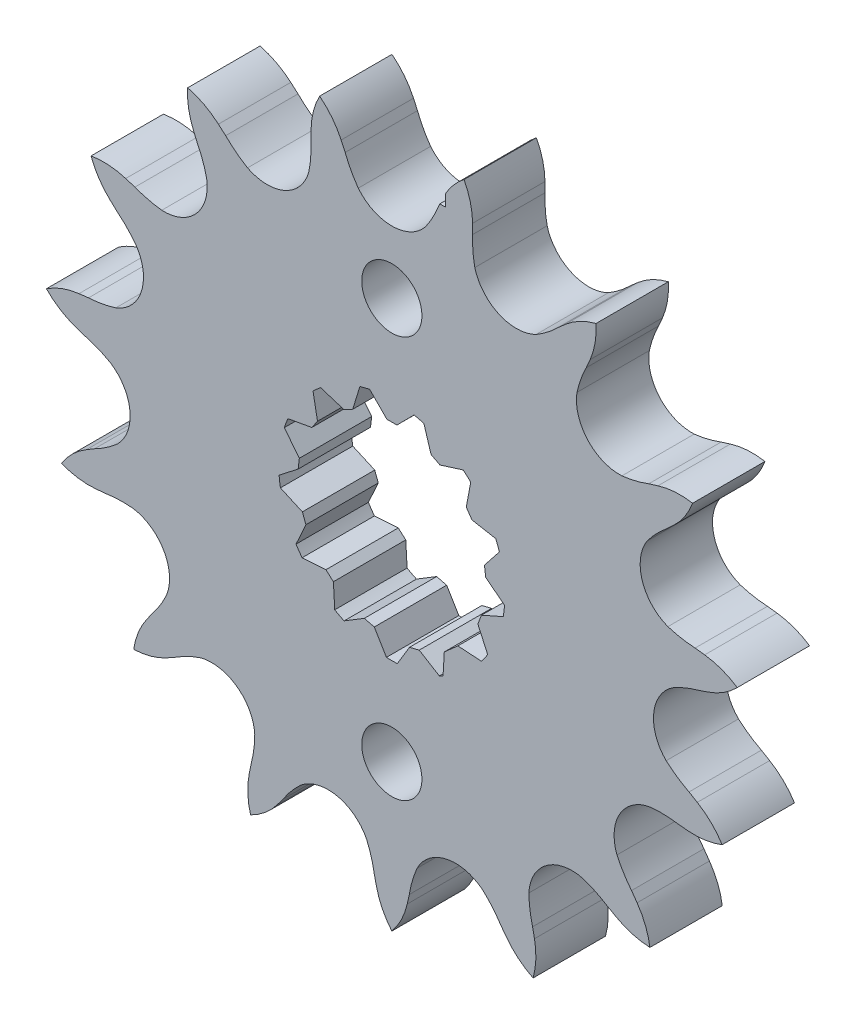
SolidWorks part; units mm, degrees
ref_plane "Front Plane" through (0, 0, 0) normal (0, 0, 1) x (1, 0, 0)
ref_plane "Top Plane" through (0, 0, 0) normal (0, 1, 0) x (1, 0, 0)
ref_plane "Right Plane" through (0, 0, 0) normal (1, 0, 0) x (0, 0, -1)
sketch "Sketch1" plane through (0, 0, 0) normal (0, 0, 1) x (1, 0, 0)
  line L0 (0, 0) -> (0, 90.9513)
  line L1 (27.8443, 30.54) -> (-27.8443, 30.54)
  line L2 (5.34, 0) -> (5.34, 90.9513)
  line L3 (27.8443, 34.869) -> (-27.8443, 34.869)
  line L4 (5.34, 34.869) -> (-3.3441, 27.8368)
  line L5 (5.34, 34.869) -> (-4.6509, 30.2665)
  line L6 (-4.6509, 30.2665) -> (-5.0517, 31.1366)
  line L7 (-11.77, 0) -> (-11.77, 90.9513)
  line L8 (27.8443, 28.037) -> (-27.8443, 28.037)
  line L9 (0, 0) -> (-8.8556, 41.6622)
  line L10 (4.6509, 30.2665) -> (5.0517, 31.1366)
  line L11 (16.5593, 25.7582) -> (17.2794, 26.39)
  line L12 (8.0617, 29.5415) -> (8.0495, 30.4995)
  line L13 (25.6045, 16.796) -> (26.5193, 17.0803)
  line L14 (19.3804, 23.7085) -> (19.7588, 24.5886)
  line L15 (30.2224, 4.9296) -> (31.1738, 4.8173)
  line L16 (27.348, 13.7761) -> (28.0517, 14.4262)
  line L17 (29.6146, -7.7891) -> (30.438, -8.2787)
  line L18 (30.5869, 1.4617) -> (31.4941, 1.7694)
  line L19 (23.8862, -19.161) -> (24.4393, -19.9432)
  line L20 (28.537, -11.1055) -> (29.491, -11.1934)
  line L21 (14.0276, -27.2198) -> (14.2148, -28.1594)
  line L22 (21.5528, -21.7524) -> (22.3886, -22.2208)
  line L23 (1.7435, -30.5721) -> (1.5324, -31.5065)
  line L24 (10.842, -28.6382) -> (11.415, -29.4059)
  line L25 (-10.842, -28.6382) -> (-11.415, -29.4059)
  line L26 (-1.7435, -30.5721) -> (-1.5324, -31.5065)
  line L27 (-21.5528, -21.7524) -> (-22.3886, -22.2208)
  line L28 (-14.0276, -27.2198) -> (-14.2148, -28.1594)
  line L29 (-28.537, -11.1055) -> (-29.491, -11.1934)
  line L30 (-23.8862, -19.161) -> (-24.4393, -19.9432)
  line L31 (-30.5869, 1.4617) -> (-31.4941, 1.7694)
  line L32 (-29.6146, -7.7891) -> (-30.438, -8.2787)
  line L33 (-27.348, 13.7761) -> (-28.0517, 14.4262)
  line L34 (-30.2224, 4.9296) -> (-31.1738, 4.8173)
  line L35 (-19.3804, 23.7085) -> (-19.7588, 24.5886)
  line L36 (-25.6045, 16.796) -> (-26.5193, 17.0803)
  line L37 (-8.0617, 29.5415) -> (-8.0495, 30.4995)
  line L38 (-16.5593, 25.7582) -> (-17.2794, 26.39)
  arc A2 (-4.6509, 30.2665) -> (-3.3441, 27.8368) centre (5.6138, 34.221) ccw
  arc A3 (-3.3441, 27.8368) -> (3.3441, 27.8368) centre (0, 30.54) ccw
  arc A4 (-5.0517, 31.1366) -> (-7.1955, 33.8523) centre (-11.77, 28.037) ccw
  arc A5 (4.6509, 30.2665) -> (3.3441, 27.8368) centre (-5.6138, 34.221) cw
  arc A6 (5.0517, 31.1366) -> (7.1955, 33.8523) centre (11.77, 28.037) cw
  arc A7 (8.2673, 26.7903) -> (14.3772, 24.07) centre (12.4217, 27.8997) ccw
  arc A8 (16.5593, 25.7582) -> (14.3772, 24.07) centre (8.7905, 33.5457) cw
  arc A9 (17.2794, 26.39) -> (20.3424, 27.9989) centre (22.1561, 20.8258) cw
  arc A10 (8.0617, 29.5415) -> (8.2673, 26.7903) centre (19.0473, 28.9791) ccw
  arc A11 (8.0495, 30.4995) -> (7.1955, 33.8523) centre (0.6512, 30.4004) ccw
  arc A12 (18.4492, 21.1116) -> (22.9244, 16.1413) centre (22.6956, 20.4352) ccw
  arc A13 (25.6045, 16.796) -> (22.9244, 16.1413) centre (21.6748, 27.0701) cw
  arc A14 (26.5193, 17.0803) -> (29.9719, 17.3043) centre (28.7112, 10.0136) cw
  arc A15 (19.3804, 23.7085) -> (18.4492, 21.1116) centre (29.1875, 18.7265) ccw
  arc A16 (19.7588, 24.5886) -> (20.3424, 27.9989) centre (12.9599, 27.5072) ccw
  arc A17 (25.441, 11.7824) -> (27.5077, 5.4217) centre (29.0453, 9.4374) ccw
  arc A18 (30.2224, 4.9296) -> (27.5077, 5.4217) centre (30.8113, 15.9139) cw
  arc A19 (31.1738, 4.8173) -> (34.419, 3.6176) centre (30.3019, -2.53) cw
  arc A20 (27.348, 13.7761) -> (25.441, 11.7824) centre (34.2808, 5.2359) ccw
  arc A21 (28.0517, 14.4262) -> (29.9719, 17.3043) centre (23.0276, 19.8578) ccw
  arc A22 (28.0338, 0.416) -> (27.3348, -6.2355) centre (30.3727, -3.1923) ccw
  arc A23 (29.6146, -7.7891) -> (27.3348, -6.2355) centre (34.6203, 2.0059) cw
  arc A24 (30.438, -8.2787) -> (32.9147, -10.6946) centre (26.6531, -14.6362) cw
  arc A25 (30.5869, 1.4617) -> (28.0338, 0.416) centre (33.4467, -9.1601) ccw
  arc A26 (31.4941, 1.7694) -> (34.419, 3.6176) centre (29.1137, 8.7749) ccw
  arc A27 (25.7794, -11.0224) -> (22.4353, -16.8144) centre (26.4484, -15.27) ccw
  arc A28 (23.8862, -19.161) -> (22.4353, -16.8144) centre (32.4431, -12.2488) cw
  arc A29 (24.4393, -19.9432) -> (25.7192, -23.1577) centre (18.3958, -24.2116) cw
  arc A30 (28.537, -11.1055) -> (25.7794, -11.0224) centre (26.8293, -21.9721) ccw
  arc A31 (29.491, -11.1934) -> (32.9147, -10.6946) centre (30.1658, -3.8254) ccw
  arc A32 (19.0675, -20.5549) -> (13.6567, -24.486) centre (17.951, -24.7074) ccw
  arc A33 (14.0276, -27.2198) -> (13.6567, -24.486) centre (24.6562, -24.3856) cw
  arc A34 (14.2148, -28.1594) -> (14.0766, -31.6165) centre (6.9576, -29.6006) cw
  arc A35 (21.5528, -21.7524) -> (19.0675, -20.5549) centre (15.5729, -30.985) ccw
  arc A36 (22.3886, -22.2208) -> (25.7192, -23.1577) centre (26.0019, -15.7642) ccw
  arc A37 (9.0586, -26.5332) -> (2.5166, -27.9238) centre (6.3496, -29.8726) ccw
  arc A38 (1.7435, -30.5721) -> (2.5166, -27.9238) centre (12.606, -32.306) cw
  arc A39 (1.5324, -31.5065) -> (0, -34.6086) centre (-5.6836, -29.8714) cw
  arc A40 (10.842, -28.6382) -> (9.0586, -26.5332) centre (1.6238, -34.6403) ccw
  arc A41 (11.415, -29.4059) -> (14.0766, -31.6165) centre (17.342, -24.9772) ccw
  arc A42 (-2.5166, -27.9238) -> (-9.0586, -26.5332) centre (-6.3496, -29.8726) ccw
  arc A43 (-10.842, -28.6382) -> (-9.0586, -26.5332) centre (-1.6238, -34.6403) cw
  arc A44 (-11.415, -29.4059) -> (-14.0766, -31.6165) centre (-17.342, -24.9772) cw
  arc A45 (-1.7435, -30.5721) -> (-2.5166, -27.9238) centre (-12.606, -32.306) ccw
  arc A46 (-1.5324, -31.5065) -> (0, -34.6086) centre (5.6836, -29.8714) ccw
  arc A47 (-13.6567, -24.486) -> (-19.0675, -20.5549) centre (-17.951, -24.7074) ccw
  arc A48 (-21.5528, -21.7524) -> (-19.0675, -20.5549) centre (-15.5729, -30.985) cw
  arc A49 (-22.3886, -22.2208) -> (-25.7192, -23.1577) centre (-26.0019, -15.7642) cw
  arc A50 (-14.0276, -27.2198) -> (-13.6567, -24.486) centre (-24.6562, -24.3856) ccw
  arc A51 (-14.2148, -28.1594) -> (-14.0766, -31.6165) centre (-6.9576, -29.6006) ccw
  arc A52 (-22.4353, -16.8144) -> (-25.7794, -11.0224) centre (-26.4484, -15.27) ccw
  arc A53 (-28.537, -11.1055) -> (-25.7794, -11.0224) centre (-26.8293, -21.9721) cw
  arc A54 (-29.491, -11.1934) -> (-32.9147, -10.6946) centre (-30.1658, -3.8254) cw
  arc A55 (-23.8862, -19.161) -> (-22.4353, -16.8144) centre (-32.4431, -12.2488) ccw
  arc A56 (-24.4393, -19.9432) -> (-25.7192, -23.1577) centre (-18.3958, -24.2116) ccw
  arc A57 (-27.3348, -6.2355) -> (-28.0338, 0.416) centre (-30.3727, -3.1923) ccw
  arc A58 (-30.5869, 1.4617) -> (-28.0338, 0.416) centre (-33.4467, -9.1601) cw
  arc A59 (-31.4941, 1.7694) -> (-34.419, 3.6176) centre (-29.1137, 8.7749) cw
  arc A60 (-29.6146, -7.7891) -> (-27.3348, -6.2355) centre (-34.6203, 2.0059) ccw
  arc A61 (-30.438, -8.2787) -> (-32.9147, -10.6946) centre (-26.6531, -14.6362) ccw
  arc A62 (-27.5077, 5.4217) -> (-25.441, 11.7824) centre (-29.0453, 9.4374) ccw
  arc A63 (-27.348, 13.7761) -> (-25.441, 11.7824) centre (-34.2808, 5.2359) cw
  arc A64 (-28.0517, 14.4262) -> (-29.9719, 17.3043) centre (-23.0276, 19.8578) cw
  arc A65 (-30.2224, 4.9296) -> (-27.5077, 5.4217) centre (-30.8113, 15.9139) ccw
  arc A66 (-31.1738, 4.8173) -> (-34.419, 3.6176) centre (-30.3019, -2.53) ccw
  arc A67 (-22.9244, 16.1413) -> (-18.4492, 21.1116) centre (-22.6956, 20.4352) ccw
  arc A68 (-19.3804, 23.7085) -> (-18.4492, 21.1116) centre (-29.1875, 18.7265) cw
  arc A69 (-19.7588, 24.5886) -> (-20.3424, 27.9989) centre (-12.9599, 27.5072) cw
  arc A70 (-25.6045, 16.796) -> (-22.9244, 16.1413) centre (-21.6748, 27.0701) ccw
  arc A71 (-26.5193, 17.0803) -> (-29.9719, 17.3043) centre (-28.7112, 10.0136) ccw
  arc A72 (-14.3772, 24.07) -> (-8.2673, 26.7903) centre (-12.4217, 27.8997) ccw
  arc A73 (-8.0617, 29.5415) -> (-8.2673, 26.7903) centre (-19.0473, 28.9791) cw
  arc A74 (-8.0495, 30.4995) -> (-7.1955, 33.8523) centre (-0.6512, 30.4004) cw
  arc A75 (-16.5593, 25.7582) -> (-14.3772, 24.07) centre (-8.7905, 33.5457) ccw
  arc A76 (-17.2794, 26.39) -> (-20.3424, 27.9989) centre (-22.1561, 20.8258) ccw
  point P7 (0, 30.54)
  dimension "D4" = 39
  dimension "D7" = 90
  dimension "D5" = 14.266
  dimension "D6" = 11
  dimension "D8" = 0.958
  dimension "D11" = 12
  dimension "D2" = 5.34
  dimension "D3" = 4.329
  dimension "D9" = 11.77
  dimension "D10" = 2.503
  dimension "D12" = 15
extrude "Boss-Extrude1" add sketch "Sketch1" along normal blind 7.21 contours L38 A76 A69 L35 A68 A67 A70 L36 A71 A64 L33 A63 A62 A65 L34 A66 A59 L31 A58 A57 A60 L32 A61 A54 L29 A53 A52 A55 L30 A56 A49 L27 A48 A47 A50 L28 A51 A44 L25 A43 A42 A45 L26 A46 A39 L23 A38 A37 A40 L24 A41 | A3 A2 L8 L9 L0 | A2 L6 L1 L9 L8 | A74 L37 A73 L8 L9 L1 | A74 L1 L9 | L6 A4 L9 L1 | L10 A5 L8 L2 L1 | L12 A11 L1 L2 L8 A10 | L1 A11 A6 L2
sketch "Sketch4" plane through (0, 0, 7.21) normal (0, 0, 1) x (1, 0, 0)
  line L1 (0, 0) -> (-0.4983, -11.3166) construction
  line L2 (0, 0) -> (-1.7465, -9.2342) construction
  line L3 (0, 0) -> (-2.7445, -8.9882) construction
  line L4 (0, 0) -> (-4.8192, -10.2513) construction
  line L5 (0, 0) -> (-5.7, -9.7889) construction
  line L6 (-0.4983, -11.3166) -> (-1.7465, -9.2342)
  line L7 (-1.7465, -9.2342) -> (-2.7445, -8.9882)
  line L8 (-2.7445, -8.9882) -> (-4.8192, -10.2513)
  line L9 (-4.8192, -10.2513) -> (-5.7, -9.7889)
  line L10 (-5.683, -9.7978) -> (-5.8209, -7.3657)
  line L11 (-5.8209, -7.3657) -> (-6.5681, -6.7038)
  line L12 (-6.5681, -6.7038) -> (-9.0003, -6.8585)
  line L13 (-9.0003, -6.8585) -> (-9.5681, -6.0358)
  line L14 (-9.5684, -6.0354) -> (-8.5602, -3.8177)
  line L15 (-8.5602, -3.8177) -> (-8.9142, -2.8844)
  line L16 (-8.9142, -2.8844) -> (-11.1398, -1.8911)
  line L17 (-11.1398, -1.8911) -> (-11.2602, -0.8988)
  line L18 (-11.2603, -0.8983) -> (-9.337, 0.5968)
  line L19 (-9.337, 0.5968) -> (-9.2167, 1.5878)
  line L20 (-9.2167, 1.5878) -> (-10.7257, 3.5016)
  line L21 (-10.7257, 3.5016) -> (-10.3712, 4.4362)
  line L22 (-10.371, 4.4366) -> (-7.9732, 4.8667)
  line L23 (-7.9732, 4.8667) -> (-7.4062, 5.6882)
  line L24 (-7.4062, 5.6882) -> (-7.853, 8.0841)
  line L25 (-7.853, 8.0841) -> (-7.1048, 8.7469)
  line L26 (-7.1044, 8.7472) -> (-4.7814, 8.0137)
  line L27 (-4.7814, 8.0137) -> (-3.8975, 8.4776)
  line L28 (-3.8975, 8.4776) -> (-3.1797, 10.8067)
  line L29 (-3.1797, 10.8067) -> (-2.2091, 11.0459)
  line L30 (-2.2087, 11.046) -> (-0.4926, 9.3169)
  line L31 (-0.4926, 9.3169) -> (0.5056, 9.317)
  line L32 (0.5056, 9.317) -> (2.2235, 11.0457)
  line L33 (2.2235, 11.0457) -> (3.1941, 10.8064)
  line L34 (3.1945, 10.8063) -> (3.9105, 8.4778)
  line L35 (3.9105, 8.4778) -> (4.7944, 8.0139)
  line L36 (4.7944, 8.0139) -> (7.1189, 8.7462)
  line L37 (7.1189, 8.7462) -> (7.8671, 8.0834)
  line L38 (7.8674, 8.083) -> (7.4193, 5.6885)
  line L39 (7.4193, 5.6885) -> (7.9864, 4.867)
  line L40 (7.9864, 4.867) -> (10.385, 4.4352)
  line L41 (10.385, 4.4352) -> (10.7394, 3.5005)
  line L42 (10.7396, 3.5001) -> (9.23, 1.5881)
  line L43 (9.23, 1.5881) -> (9.3503, 0.5972)
  line L44 (9.3503, 0.5972) -> (11.2735, -0.8999)
  line L45 (11.2735, -0.8999) -> (11.153, -1.8922)
  line L46 (11.1529, -1.8926) -> (8.9277, -2.8841)
  line L47 (8.9277, -2.8841) -> (8.5738, -3.8174)
  line L48 (8.5738, -3.8174) -> (9.5809, -6.0367)
  line L49 (9.5809, -6.0367) -> (9.0131, -6.8593)
  line L50 (9.0128, -6.8597) -> (6.5817, -6.7035)
  line L51 (6.5817, -6.7035) -> (5.2276, -7.9031)
  line L52 (5.2276, -7.9031) -> (5.101, -10.1103)
  line L53 (5.101, -10.1103) -> (4.8099, -10.2631)
  line L54 (4.8095, -10.2633) -> (2.7295, -8.9952)
  line L55 (2.7295, -8.9952) -> (1.7603, -9.2341)
  line L56 (1.7603, -9.2341) -> (0.5059, -11.3237)
  line L57 (0.5059, -11.3237) -> (-0.4936, -11.3237)
  circle A2 centre (0, 0) radius 11.2646
extrude "Cut-Extrude1" cut sketch "Sketch4" against normal through all contours L42 A2 L40 L39 L38 L36 L35 L34 L33 L32 L31 L30 L29 L28 L27 L26 L25 L24 L23 L22 L20 L19 L18 L16 L15 L14 L12 L11 L10 L8 L7 L6 L56 L55 L54 L52 L51 L50
sketch "Sketch5" plane through (0, 0, 7.21) normal (0, 0, 1) x (1, 0, 0)
  circle A0 centre (0, 0) radius 20
  circle A1 centre (0, 20) radius 3
  circle A2 centre (0, -20) radius 3
  dimension "D1" = 40
  dimension "D2" = 6
  dimension "D3" = 6
extrude "Cut-Extrude2" cut sketch "Sketch5" against normal through all contours A0 A1 | A0 A1 | A0 A2 | A0 A2
